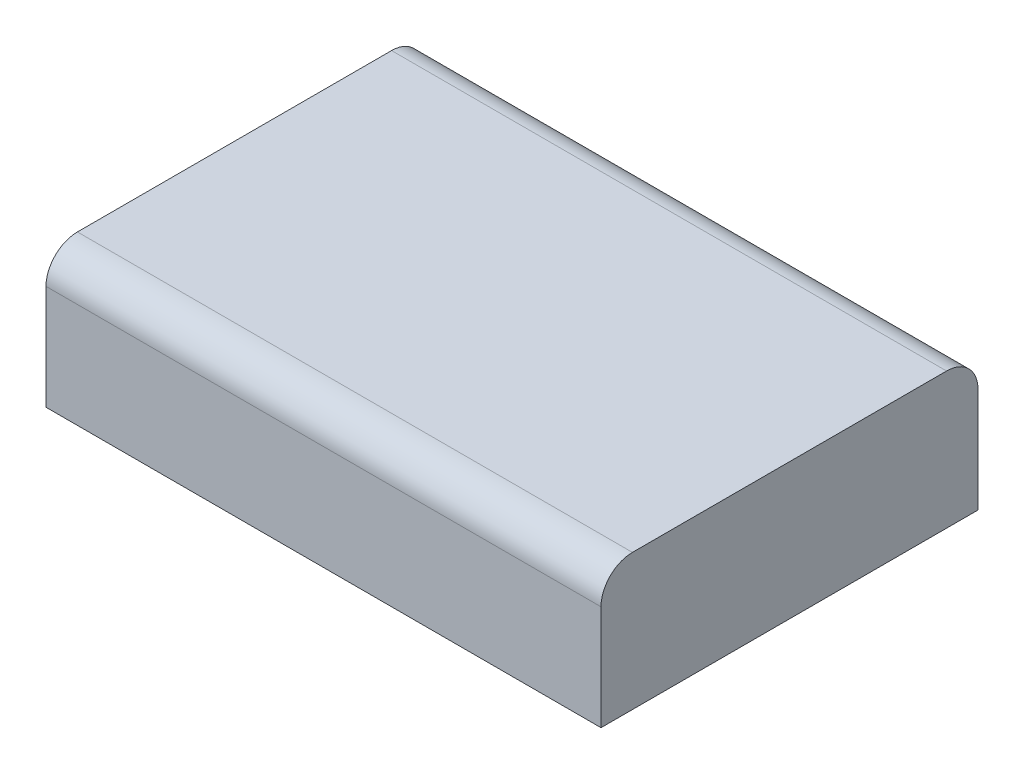
SolidWorks part; units mm, degrees
ref_plane "Front Plane" through (0, 0, 0) normal (0, 0, 1) x (1, 0, 0)
ref_plane "Top Plane" through (0, 0, 0) normal (0, 1, 0) x (1, 0, 0)
ref_plane "Right Plane" through (0, 0, 0) normal (1, 0, 0) x (0, 0, -1)
sketch "Sketch1" plane through (0, 0, 0) normal (0, 1, 0) x (1, 0, 0)
  line L1 (-26.5, -18) -> (26.5, -18)
  line L2 (-26.5, -18) -> (-26.5, 18)
  line L3 (-26.5, 18) -> (26.5, 18)
  line L4 (26.5, -18) -> (26.5, 18)
  line L5 (-26.5, -18) -> (26.5, 18) construction
  line L6 (-26.5, 18) -> (26.5, -18) construction
  point P0 (0, 0)
  dimension "D1" = 53
  dimension "D2" = 36
extrude "Boss-Extrude1" add sketch "Sketch1" along normal blind 13
sketch "Sketch2" plane through (26.5, 0, 0) normal (1, 0, 0) x (0, 0, -1)
  line L0 (-18, 13) -> (-15, 13)
  line L1 (-18, 13) -> (-18, 10)
  line L2 (15, 13) -> (18, 13)
  line L3 (18, 13) -> (18, 10)
  arc A0 (-15, 13) -> (-18, 10) centre (-15, 10) ccw
  arc A1 (18, 10) -> (15, 13) centre (15, 10) ccw
  dimension "D2" = 3
  dimension "D3" = 3
extrude "Cut-Extrude1" cut sketch "Sketch2" against normal through all
